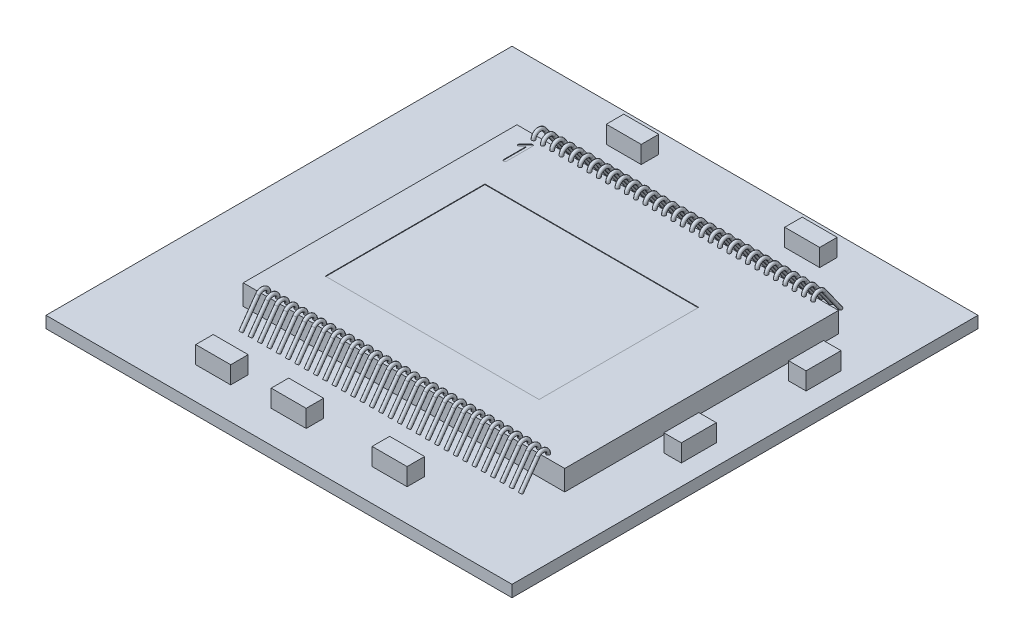
SolidWorks part; units mm, degrees
material "1060 Legierung"
ref_plane "Vorne" through (0, 0, 0) normal (0, 0, 1) x (1, 0, 0)
ref_plane "Oben" through (0, 0, 0) normal (0, 1, 0) x (1, 0, 0)
ref_plane "Rechts" through (0, 0, 0) normal (1, 0, 0) x (0, 0, -1)
ref_plane "Faser-Ebene_Vorne" through (0, 0, 0.175) normal (0, 0, 1) x (1, 0, 0)
ref_plane "Faser-Ebene_Rechts" through (-0.32, 0, 0) normal (1, 0, 0) x (0, 0, -1)
sketch "Skizze1" plane through (0, 0, 0) normal (0, 1, 0) x (1, 0, 0)
  line L0 (-2.76, 2.35) -> (2.76, -2.35) construction
  line L1 (-2.76, 2.35) -> (2.76, 2.35)
  line L2 (-2.76, 2.35) -> (-2.76, -2.35)
  line L3 (-2.76, -2.35) -> (2.76, -2.35)
  line L4 (2.76, 2.35) -> (2.76, -2.35)
extrude "Chip_Die" add sketch "Skizze1" along normal blind 0.35
sketch "Skizze4" plane through (0, 0.35, 0) normal (0, 1, 0) x (1, 0, 0)
  line L1 (-2.155, 1.195) -> (1.515, 1.195)
  line L2 (-2.155, 1.195) -> (-2.155, -1.545)
  line L3 (-2.155, -1.545) -> (1.515, -1.545)
  line L4 (1.515, 1.195) -> (1.515, -1.545)
  line L5 (-0.32, 1.195) -> (-0.32, -0.1113) construction
  line L7 (-0.32, -0.1925) -> (-0.32, 0.1925) construction
  line L8 (1.515, -0.175) -> (0.7734, -0.175) construction
  line L9 (-0.1925, -0.175) -> (0.1925, -0.175) construction
extrude "Active_Area" cut sketch "Skizze4" against normal blind 0.01
sketch "Skizze5" plane through (0, 0.35, 0) normal (0, 1, 0) x (1, 0, 0)
  text T0 "1" font "ISOCPEUR" height 0.5
extrude "Pin1" cut sketch "Skizze5" against normal blind 0.01
sketch "Skizze6" plane through (0, 0, 0) normal (0, 1, 0) x (1, 0, 0)
  line L0 (-2.155, 1.195) -> (1.515, -1.545) construction
  line L1 (-4.32, 3.825) -> (3.68, 3.825)
  line L2 (-4.32, 3.825) -> (-4.32, -4.175)
  line L3 (-4.32, -4.175) -> (3.68, -4.175)
  line L4 (3.68, 3.825) -> (3.68, -4.175)
  line L5 (3.68, 3.825) -> (-4.32, -4.175) construction
  point P7 (-0.32, -0.175)
extrude "Base-Plate" add sketch "Skizze6" against normal blind 0.2
sketch "Skizze12" plane through (0, 0, 0) normal (1, 0, 0) x (0, 0, -1)
  line L0 (-2.35, 0.35) -> (2.35, 0.35) construction
  line L1 (-2.4563, 0.4079) -> (-2.7458, 0)
  line L2 (-4.175, 0) -> (3.825, 0) construction
  line L3 (0, 0) -> (0, 1.1196) construction
  arc A0 (-2.2748, 0.35) -> (-2.4563, 0.4079) centre (-2.3748, 0.35) ccw
sketch "Skizze13" plane through (0, 0.35, 0) normal (0, 1, 0) x (1, 0, 0)
  line L0 (0, 0) -> (0, -1.1473) construction
  circle A0 centre (0, -2.2748) radius 0.03
  circle A1 centre (0.16, -2.2748) radius 0.03
  circle A2 centre (0.32, -2.2748) radius 0.03
  circle A3 centre (0.48, -2.2748) radius 0.03
  circle A4 centre (0.64, -2.2748) radius 0.03
  circle A5 centre (0.8, -2.2748) radius 0.03
  circle A6 centre (0.96, -2.2748) radius 0.03
  circle A7 centre (1.12, -2.2748) radius 0.03
  circle A8 centre (1.28, -2.2748) radius 0.03
  circle A9 centre (1.44, -2.2748) radius 0.03
  circle A10 centre (1.6, -2.2748) radius 0.03
  circle A11 centre (1.76, -2.2748) radius 0.03
  circle A12 centre (1.92, -2.2748) radius 0.03
  circle A13 centre (2.08, -2.2748) radius 0.03
  circle A14 centre (2.24, -2.2748) radius 0.03
  circle A15 centre (2.4, -2.2748) radius 0.03
  circle A16 centre (-2.4, -2.2748) radius 0.03
  circle A17 centre (-2.24, -2.2748) radius 0.03
  circle A18 centre (-2.08, -2.2748) radius 0.03
  circle A19 centre (-1.92, -2.2748) radius 0.03
  circle A20 centre (-1.76, -2.2748) radius 0.03
  circle A21 centre (-1.6, -2.2748) radius 0.03
  circle A22 centre (-1.44, -2.2748) radius 0.03
  circle A23 centre (-1.28, -2.2748) radius 0.03
  circle A24 centre (-1.12, -2.2748) radius 0.03
  circle A25 centre (-0.96, -2.2748) radius 0.03
  circle A26 centre (-0.8, -2.2748) radius 0.03
  circle A27 centre (-0.64, -2.2748) radius 0.03
  circle A28 centre (-0.48, -2.2748) radius 0.03
  circle A29 centre (-0.32, -2.2748) radius 0.03
  circle A30 centre (-0.16, -2.2748) radius 0.03
sweep "Bonding-wires" add profiles "Skizze13" path "Skizze12"
mirror "Spiegeln1" about plane through (0, 0, 0) normal (0, 0, 1) of "Bonding-wires"
sketch "Skizze14" plane through (0, 0, 0) normal (0, 1, 0) x (1, 0, 0)
  line L0 (-4.32, -4.175) -> (3.68, -4.175) construction
  line L1 (-2.2994, -3.325) -> (-1.6994, -3.325)
  line L2 (-2.2994, -3.325) -> (-2.2994, -3.625)
  line L3 (-2.2994, -3.625) -> (-1.6994, -3.625)
  line L4 (-1.6994, -3.325) -> (-1.6994, -3.625)
  line L5 (3.68, -4.175) -> (3.68, 3.825) construction
  line L6 (-1.0036, -3.325) -> (-0.4036, -3.325)
  line L7 (-1.0036, -3.325) -> (-1.0036, -3.625)
  line L8 (-1.0036, -3.625) -> (-0.4036, -3.625)
  line L9 (-0.4036, -3.325) -> (-0.4036, -3.625)
  line L10 (0.7291, -3.625) -> (1.3291, -3.625)
  line L11 (0.7291, -3.625) -> (0.7291, -3.325)
  line L12 (0.7291, -3.325) -> (1.3291, -3.325)
  line L13 (1.3291, -3.625) -> (1.3291, -3.325)
  line L14 (3.03, -0.3181) -> (3.33, -0.3181)
  line L15 (3.03, -0.3181) -> (3.03, -0.9181)
  line L16 (3.03, -0.9181) -> (3.33, -0.9181)
  line L17 (3.33, -0.3181) -> (3.33, -0.9181)
  line L18 (3.68, 3.825) -> (-4.32, 3.825) construction
  line L19 (3.03, 1.2236) -> (3.33, 1.2236)
  line L20 (3.03, 1.2236) -> (3.03, 1.8236)
  line L21 (3.03, 1.8236) -> (3.33, 1.8236)
  line L22 (3.33, 1.2236) -> (3.33, 1.8236)
  line L23 (-1.4515, 3.175) -> (-2.0515, 3.175)
  line L24 (-1.4515, 3.175) -> (-1.4515, 3.475)
  line L25 (-1.4515, 3.475) -> (-2.0515, 3.475)
  line L26 (-2.0515, 3.175) -> (-2.0515, 3.475)
  line L28 (1.012, 3.475) -> (1.612, 3.475)
  line L29 (1.012, 3.475) -> (1.012, 3.175)
  line L30 (1.012, 3.175) -> (1.612, 3.175)
  line L31 (1.612, 3.475) -> (1.612, 3.175)
extrude "Electronic_components" add sketch "Skizze14" along normal blind 0.3
